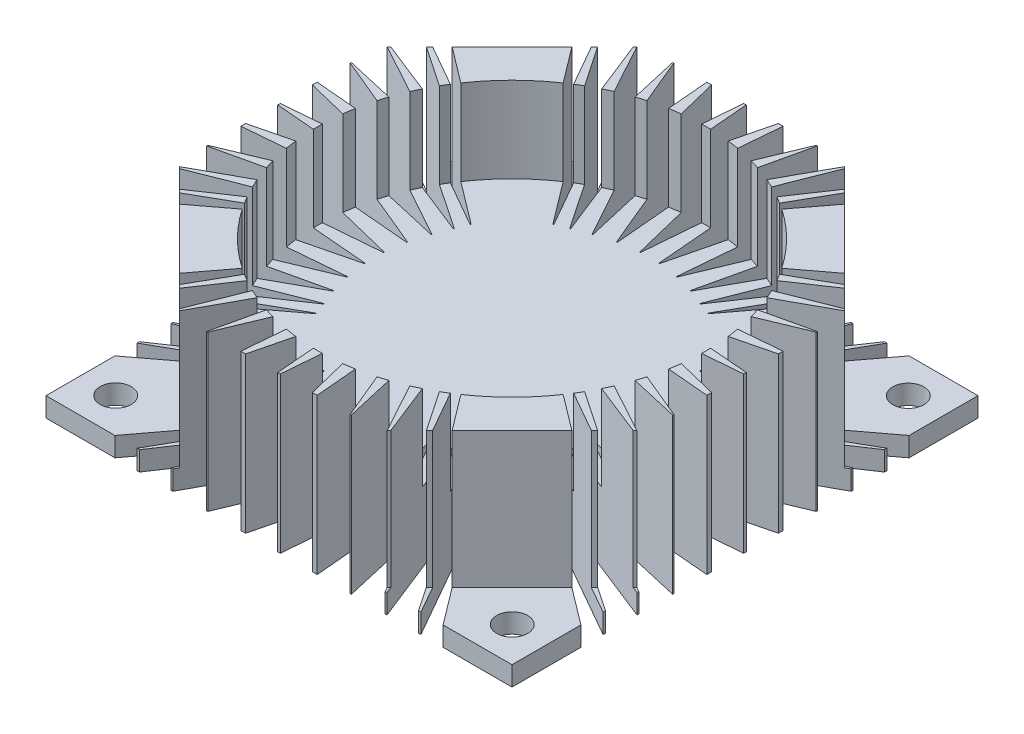
SolidWorks part; units mm, degrees
ref_plane "前视基准面" through (0, 0, 0) normal (0, 0, 1) x (1, 0, 0)
ref_plane "上视基准面" through (0, 0, 0) normal (0, 1, 0) x (1, 0, 0)
ref_plane "右视基准面" through (0, 0, 0) normal (1, 0, 0) x (0, 0, -1)
sketch "草图1" plane through (0, 0, 0) normal (0, 1, 0) x (1, 0, 0)
  line L1 (-30, 30) -> (30, 30)
  line L2 (-30, 30) -> (-30, -30)
  line L3 (-30, -30) -> (30, -30)
  line L4 (30, 30) -> (30, -30)
  line L5 (-30, 30) -> (30, -30) construction
  line L6 (-30, -30) -> (30, 30) construction
  point P0 (0, 0)
  dimension "D1" = 60
  dimension "D2" = 60
extrude "凸台-拉伸1" add sketch "草图1" along normal blind 20
sketch "草图2" plane through (0, 20, 0) normal (0, 1, 0) x (1, 0, 0)
  line L0 (0, 32.7009) -> (0, -33.3723) construction
  line L1 (-34.1781, 0) -> (33.7081, 0) construction
  line L2 (30, 30) -> (12.78, 30)
  line L3 (30, 30) -> (-30, 30) construction
  line L4 (12.78, 30) -> (30, 12.78)
  line L5 (30, -30) -> (30, 30) construction
  line L6 (30, 12.78) -> (30, 30)
  line L7 (12.78, -30) -> (30, -12.78)
  line L8 (30, -30) -> (12.78, -30)
  line L9 (30, -12.78) -> (30, -30)
  line L10 (-30, -30) -> (-12.78, -30)
  line L11 (-30, -12.78) -> (-30, -30)
  line L12 (-12.78, -30) -> (-30, -12.78)
  line L13 (-12.78, 30) -> (-30, 12.78)
  line L14 (-30, 30) -> (-12.78, 30)
  line L15 (-30, 12.78) -> (-30, 30)
  point P10 (0, 0)
  point P14 (0, 0)
  point P15 (30, 14.4663)
  dimension "D1" = 17.22
  dimension "D2" = 17.22
extrude "切除-拉伸1" cut sketch "草图2" against normal blind 17.5
sketch "草图3" plane through (0, 20, 0) normal (0, 1, 0) x (1, 0, 0)
  circle A0 centre (0, 0) radius 25
  dimension "D1" = 50
extrude "切除-拉伸2" cut sketch "草图3" against normal blind 11
sketch "草图5" plane through (0, 0, 0) normal (0, -1, 0) x (1, 0, 0)
  line L0 (0, 0) -> (30, -30) construction
  line L1 (0, 34.6469) -> (0, -34.1363) construction
  line L2 (32.3775, 0) -> (-31.3, 0) construction
  line L3 (0, 0) -> (34.3568, -22.3531) construction
  line L5 (0, 0) -> (34.3568, -18.1325) construction
  line L6 (0, 0) -> (35.3814, -13.3048) construction
  line L7 (0, 0) -> (35.3814, -7.8488) construction
  line L8 (0, 0) -> (35.2377, -2.4458) construction
  line L9 (30, -21.13) -> (15.2833, -10.0082)
  line L10 (30, 30) -> (30, -30) construction
  line L12 (30, -17.96) -> (15.8572, -8.4247)
  line L13 (15.9036, -8.3368) -> (30, -13.9041)
  line L14 (30, -13.6759) -> (16.684, -6.3605)
  line L15 (16.7193, -6.2679) -> (30, -9.3137)
  line L16 (17.3821, -3.9139) -> (30, -9.1702)
  line L17 (17.4057, -3.8179) -> (30, -4.914)
  line L19 (17.7617, -1.1863) -> (30, -0.1615)
  line L20 (30, -9.1702) -> (30, -4.914)
  line L21 (30, -9.3137) -> (30, -13.6759)
  line L22 (30, -13.9041) -> (30, -17.96)
  line L24 (15.3382, -9.9249) -> (30, -18.2721)
  line L25 (30, -18.2721) -> (30, -21.13)
  line L26 (17.7539, -1.2847) -> (30, -4.3031)
  line L27 (30, -4.3031) -> (30, -0.1615)
  line L29 (18.2721, -30) -> (21.13, -30)
  line L30 (9.9249, -15.3382) -> (18.2721, -30)
  line L31 (21.13, -30) -> (10.0082, -15.2833)
  line L32 (1.2847, -17.7539) -> (4.3031, -30)
  line L33 (1.1863, -17.7617) -> (0.1615, -30)
  line L34 (4.3031, -30) -> (0.1615, -30)
  line L35 (3.9139, -17.3821) -> (9.1702, -30)
  line L36 (3.8179, -17.4057) -> (4.914, -30)
  line L37 (9.1702, -30) -> (4.914, -30)
  line L38 (6.2679, -16.7193) -> (9.3137, -30)
  line L39 (13.6759, -30) -> (6.3605, -16.684)
  line L40 (9.3137, -30) -> (13.6759, -30)
  line L41 (8.3368, -15.9036) -> (13.9041, -30)
  line L42 (17.96, -30) -> (8.4247, -15.8572)
  line L43 (13.9041, -30) -> (17.96, -30)
  line L44 (-17.7539, -1.2847) -> (-30, -4.3031)
  line L45 (-17.7617, -1.1863) -> (-30, -0.1615)
  line L46 (-30, -4.3031) -> (-30, -0.1615)
  line L47 (-17.3821, -3.9139) -> (-30, -9.1702)
  line L48 (-17.4057, -3.8179) -> (-30, -4.914)
  line L49 (-30, -9.1702) -> (-30, -4.914)
  line L50 (-16.7193, -6.2679) -> (-30, -9.3137)
  line L51 (-30, -13.6759) -> (-16.684, -6.3605)
  line L52 (-30, -9.3137) -> (-30, -13.6759)
  line L53 (-15.9036, -8.3368) -> (-30, -13.9041)
  line L54 (-30, -17.96) -> (-15.8572, -8.4247)
  line L55 (-30, -13.9041) -> (-30, -17.96)
  line L56 (-30, -18.2721) -> (-30, -21.13)
  line L57 (-15.3382, -9.9249) -> (-30, -18.2721)
  line L58 (-30, -21.13) -> (-15.2833, -10.0082)
  line L59 (-9.9249, -15.3382) -> (-18.2721, -30)
  line L60 (-21.13, -30) -> (-10.0082, -15.2833)
  line L61 (-18.2721, -30) -> (-21.13, -30)
  line L62 (-17.96, -30) -> (-8.4247, -15.8572)
  line L63 (-13.9041, -30) -> (-17.96, -30)
  line L64 (-8.3368, -15.9036) -> (-13.9041, -30)
  line L65 (-13.6759, -30) -> (-6.3605, -16.684)
  line L66 (-9.3137, -30) -> (-13.6759, -30)
  line L67 (-6.2679, -16.7193) -> (-9.3137, -30)
  line L68 (-3.8179, -17.4057) -> (-4.914, -30)
  line L69 (-9.1702, -30) -> (-4.914, -30)
  line L70 (-3.9139, -17.3821) -> (-9.1702, -30)
  line L71 (-1.1863, -17.7617) -> (-0.1615, -30)
  line L72 (-4.3031, -30) -> (-0.1615, -30)
  line L73 (-1.2847, -17.7539) -> (-4.3031, -30)
  line L74 (17.7539, 1.2847) -> (30, 4.3031)
  line L75 (17.7617, 1.1863) -> (30, 0.1615)
  line L76 (30, 4.3031) -> (30, 0.1615)
  line L77 (17.3821, 3.9139) -> (30, 9.1702)
  line L78 (17.4057, 3.8179) -> (30, 4.914)
  line L79 (30, 9.1702) -> (30, 4.914)
  line L80 (16.7193, 6.2679) -> (30, 9.3137)
  line L81 (30, 13.6759) -> (16.684, 6.3605)
  line L82 (30, 9.3137) -> (30, 13.6759)
  line L83 (15.9036, 8.3368) -> (30, 13.9041)
  line L84 (30, 17.96) -> (15.8572, 8.4247)
  line L85 (30, 13.9041) -> (30, 17.96)
  line L86 (30, 18.2721) -> (30, 21.13)
  line L87 (15.3382, 9.9249) -> (30, 18.2721)
  line L88 (30, 21.13) -> (15.2833, 10.0082)
  line L89 (9.9249, 15.3382) -> (18.2721, 30)
  line L90 (21.13, 30) -> (10.0082, 15.2833)
  line L91 (18.2721, 30) -> (21.13, 30)
  line L92 (17.96, 30) -> (8.4247, 15.8572)
  line L93 (13.9041, 30) -> (17.96, 30)
  line L94 (8.3368, 15.9036) -> (13.9041, 30)
  line L95 (13.6759, 30) -> (6.3605, 16.684)
  line L96 (9.3137, 30) -> (13.6759, 30)
  line L97 (6.2679, 16.7193) -> (9.3137, 30)
  line L98 (3.8179, 17.4057) -> (4.914, 30)
  line L99 (9.1702, 30) -> (4.914, 30)
  line L100 (3.9139, 17.3821) -> (9.1702, 30)
  line L101 (1.1863, 17.7617) -> (0.1615, 30)
  line L102 (4.3031, 30) -> (0.1615, 30)
  line L103 (1.2847, 17.7539) -> (4.3031, 30)
  line L104 (-1.2847, 17.7539) -> (-4.3031, 30)
  line L105 (-4.3031, 30) -> (-0.1615, 30)
  line L106 (-1.1863, 17.7617) -> (-0.1615, 30)
  line L107 (-3.9139, 17.3821) -> (-9.1702, 30)
  line L108 (-9.1702, 30) -> (-4.914, 30)
  line L109 (-3.8179, 17.4057) -> (-4.914, 30)
  line L110 (-13.6759, 30) -> (-6.3605, 16.684)
  line L111 (-9.3137, 30) -> (-13.6759, 30)
  line L112 (-6.2679, 16.7193) -> (-9.3137, 30)
  line L113 (-17.96, 30) -> (-8.4247, 15.8572)
  line L114 (-13.9041, 30) -> (-17.96, 30)
  line L115 (-8.3368, 15.9036) -> (-13.9041, 30)
  line L116 (-21.13, 30) -> (-10.0082, 15.2833)
  line L117 (-18.2721, 30) -> (-21.13, 30)
  line L118 (-9.9249, 15.3382) -> (-18.2721, 30)
  line L119 (-15.3382, 9.9249) -> (-30, 18.2721)
  line L120 (-30, 21.13) -> (-15.2833, 10.0082)
  line L121 (-30, 18.2721) -> (-30, 21.13)
  line L122 (-30, 17.96) -> (-15.8572, 8.4247)
  line L123 (-30, 13.9041) -> (-30, 17.96)
  line L124 (-15.9036, 8.3368) -> (-30, 13.9041)
  line L125 (-30, 13.6759) -> (-16.684, 6.3605)
  line L126 (-30, 9.3137) -> (-30, 13.6759)
  line L127 (-16.7193, 6.2679) -> (-30, 9.3137)
  line L128 (-17.4057, 3.8179) -> (-30, 4.914)
  line L129 (-30, 9.1702) -> (-30, 4.914)
  line L130 (-17.3821, 3.9139) -> (-30, 9.1702)
  line L131 (-17.7617, 1.1863) -> (-30, 0.1615)
  line L132 (-30, 4.3031) -> (-30, 0.1615)
  line L133 (-17.7539, 1.2847) -> (-30, 4.3031)
  arc A0 (15.2833, -10.0082) -> (15.3382, -9.9249) centre (15.3135, -9.9683) cw
  arc A1 (17.7539, -1.2847) -> (17.7617, -1.1863) centre (17.7659, -1.2362) cw
  arc A2 (17.3821, -3.9139) -> (17.4057, -3.8179) centre (17.4013, -3.8677) cw
  arc A3 (16.684, -6.3605) -> (16.7193, -6.2679) centre (16.7081, -6.3167) cw
  arc A4 (15.8572, -8.4247) -> (15.9036, -8.3368) centre (15.8852, -8.3833) cw
  arc A5 (10.0082, -15.2833) -> (9.9249, -15.3382) centre (9.9683, -15.3135) ccw
  arc A6 (1.2847, -17.7539) -> (1.1863, -17.7617) centre (1.2362, -17.7659) ccw
  arc A7 (3.9139, -17.3821) -> (3.8179, -17.4057) centre (3.8677, -17.4013) ccw
  arc A8 (6.3605, -16.684) -> (6.2679, -16.7193) centre (6.3167, -16.7081) ccw
  arc A9 (8.4247, -15.8572) -> (8.3368, -15.9036) centre (8.3833, -15.8852) ccw
  arc A10 (-17.7539, -1.2847) -> (-17.7617, -1.1863) centre (-17.7659, -1.2362) ccw
  arc A11 (-17.3821, -3.9139) -> (-17.4057, -3.8179) centre (-17.4013, -3.8677) ccw
  arc A12 (-16.684, -6.3605) -> (-16.7193, -6.2679) centre (-16.7081, -6.3167) ccw
  arc A13 (-15.8572, -8.4247) -> (-15.9036, -8.3368) centre (-15.8852, -8.3833) ccw
  arc A14 (-15.2833, -10.0082) -> (-15.3382, -9.9249) centre (-15.3135, -9.9683) ccw
  arc A15 (-10.0082, -15.2833) -> (-9.9249, -15.3382) centre (-9.9683, -15.3135) cw
  arc A16 (-8.4247, -15.8572) -> (-8.3368, -15.9036) centre (-8.3833, -15.8852) cw
  arc A17 (-6.3605, -16.684) -> (-6.2679, -16.7193) centre (-6.3167, -16.7081) cw
  arc A18 (-3.9139, -17.3821) -> (-3.8179, -17.4057) centre (-3.8677, -17.4013) cw
  arc A19 (-1.2847, -17.7539) -> (-1.1863, -17.7617) centre (-1.2362, -17.7659) cw
  arc A20 (17.7539, 1.2847) -> (17.7617, 1.1863) centre (17.7659, 1.2362) ccw
  arc A21 (17.3821, 3.9139) -> (17.4057, 3.8179) centre (17.4013, 3.8677) ccw
  arc A22 (16.684, 6.3605) -> (16.7193, 6.2679) centre (16.7081, 6.3167) ccw
  arc A23 (15.8572, 8.4247) -> (15.9036, 8.3368) centre (15.8852, 8.3833) ccw
  arc A24 (15.2833, 10.0082) -> (15.3382, 9.9249) centre (15.3135, 9.9683) ccw
  arc A25 (10.0082, 15.2833) -> (9.9249, 15.3382) centre (9.9683, 15.3135) cw
  arc A26 (8.4247, 15.8572) -> (8.3368, 15.9036) centre (8.3833, 15.8852) cw
  arc A27 (6.3605, 16.684) -> (6.2679, 16.7193) centre (6.3167, 16.7081) cw
  arc A28 (3.9139, 17.3821) -> (3.8179, 17.4057) centre (3.8677, 17.4013) cw
  arc A29 (1.2847, 17.7539) -> (1.1863, 17.7617) centre (1.2362, 17.7659) cw
  arc A30 (-1.2847, 17.7539) -> (-1.1863, 17.7617) centre (-1.2362, 17.7659) ccw
  arc A31 (-3.9139, 17.3821) -> (-3.8179, 17.4057) centre (-3.8677, 17.4013) ccw
  arc A32 (-6.3605, 16.684) -> (-6.2679, 16.7193) centre (-6.3167, 16.7081) ccw
  arc A33 (-8.4247, 15.8572) -> (-8.3368, 15.9036) centre (-8.3833, 15.8852) ccw
  arc A34 (-10.0082, 15.2833) -> (-9.9249, 15.3382) centre (-9.9683, 15.3135) ccw
  arc A35 (-15.2833, 10.0082) -> (-15.3382, 9.9249) centre (-15.3135, 9.9683) cw
  arc A36 (-15.8572, 8.4247) -> (-15.9036, 8.3368) centre (-15.8852, 8.3833) cw
  arc A37 (-16.684, 6.3605) -> (-16.7193, 6.2679) centre (-16.7081, 6.3167) cw
  arc A38 (-17.3821, 3.9139) -> (-17.4057, 3.8179) centre (-17.4013, 3.8677) cw
  arc A39 (-17.7539, 1.2847) -> (-17.7617, 1.1863) centre (-17.7659, 1.2362) cw
  point P18 (0, 0)
  point P32 (13.9024, -10.6288)
  point P33 (13.4572, -11.1873)
  point P34 (0, 0)
  point P35 (13.8297, -10.7233)
  point P36 (30, -18.7042)
  point P37 (35.1447, -17.6479)
  point P38 (30, -17.96)
  point P39 (30, -18.2721)
  point P40 (34.9809, -22.7372)
  point P41 (34.3568, -22.3531)
  point P42 (34.3568, -18.2721)
  point P43 (34.3568, -18.1325)
  point P44 (30, -4.3031)
  point P45 (30, -4.914)
  point P46 (30, 0)
  point P47 (0, 0)
  point P48 (0, 0)
  point P49 (30, -0.1615)
  point P125 (0, 0)
  point P126 (35.3814, -13.3048)
  point P156 (14.6686, -9.5437)
  point P159 (17.458, -1.2118)
  point P162 (17.0847, -3.79)
  point P165 (16.3695, -6.1877)
  point P168 (15.4768, -8.1682)
  point P169 (0, 0)
  point P170 (23.5662, -8.3368)
  dimension "D1" = 0.05
  dimension "D3" = 0.05
  dimension "D2" = 8.87
extrude "切除-拉伸11" cut sketch "草图5" against normal through all
sketch "草图8" plane through (0, 0, 0) normal (0, -1, 0) x (1, 0, 0)
  line L0 (-36.0358, 0) -> (33.4059, 0) construction
  line L1 (0, 33.5523) -> (0, -33.4556) construction
  circle A0 centre (25.5268, 25.5) radius 2
  circle A1 centre (25.5268, -25.5) radius 2
  circle A2 centre (-25.5268, -25.5) radius 2
  circle A3 centre (-25.5268, 25.5) radius 2
  dimension "D2" = 4
  dimension "D1" = 25.5
extrude "切除-拉伸12" cut sketch "草图8" against normal through all
